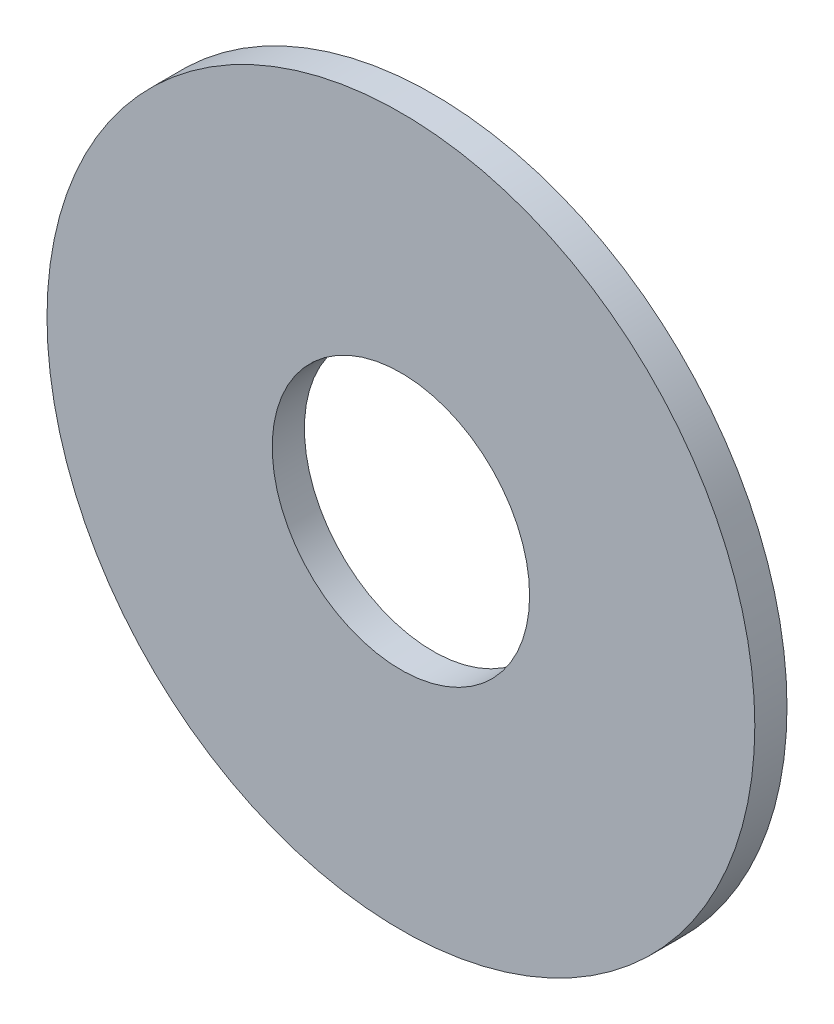
SolidWorks part; units mm, degrees
ref_plane "Face" through (0, 0, 0) normal (0, 0, 1) x (1, 0, 0)
ref_plane "Dessus" through (0, 0, 0) normal (0, 1, 0) x (1, 0, 0)
ref_plane "Droite" through (0, 0, 0) normal (1, 0, 0) x (0, 0, -1)
sketch "Esquisse1" plane through (0, 0, 0) normal (0, 0, 1) x (1, 0, 0)
  circle A0 centre (0, 0) radius 4
  circle A1 centre (0, 0) radius 11
  dimension "D1" = 8
  dimension "D2" = 22
extrude "Extrusion1" add sketch "Esquisse1" along normal blind 1
